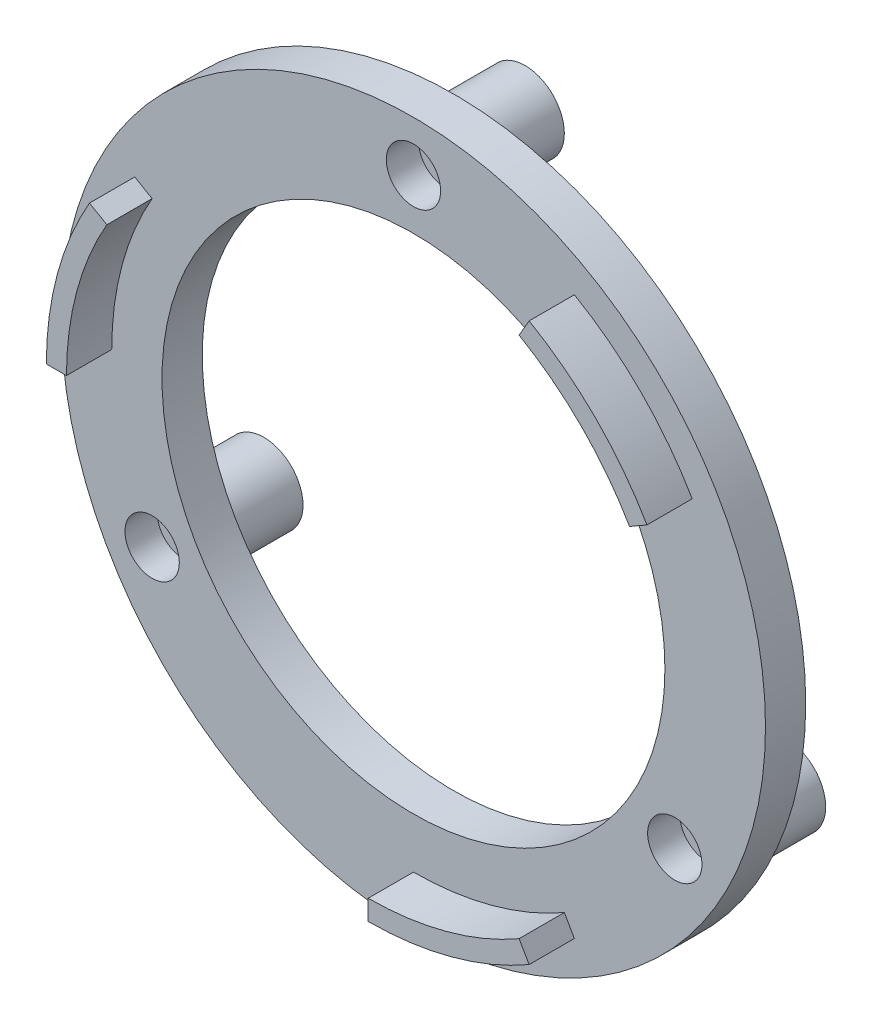
SolidWorks part; units mm, degrees
ref_plane "Front Plane" through (0, 0, 0) normal (0, 0, 1) x (1, 0, 0)
ref_plane "Top Plane" through (0, 0, 0) normal (0, 1, 0) x (1, 0, 0)
ref_plane "Right Plane" through (0, 0, 0) normal (1, 0, 0) x (0, 0, -1)
sketch "Sketch1" plane through (0, 0, 0) normal (0, 0, 1) x (1, 0, 0)
  circle A0 centre (0, 0) radius 30
  circle A1 centre (0, 0) radius 35
  circle A2 centre (0, 0) radius 25
  dimension "D1" = 5
  dimension "D2" = 5
extrude "Boss-Extrude1" add sketch "Sketch1" along normal blind 4 contours A1 A0 | A0 A2
sketch "Sketch2" plane through (0, 0, 0) normal (0, 0, -1) x (-1, 0, 0)
  circle A0 centre (0, 0) radius 30
  circle A1 centre (0, 30) radius 3.9
  circle A5 centre (25.9808, -15) radius 3.9
  circle A6 centre (-25.9808, -15) radius 3.9
  point P12 (0, 0)
  point P14 (0, 0)
  dimension "D1" = 3
extrude "Boss-Extrude2" add sketch "Sketch2" along normal blind 7.1 contours A1 | A6 | A5
sketch "Sketch3" plane through (0, 0, -7.1) normal (0, 0, -1) x (-1, 0, 0)
  circle A0 centre (0, 30) radius 1.6
  circle A4 centre (25.9808, -15) radius 1.6
  circle A5 centre (-25.9808, -15) radius 1.6
  point P10 (0, 0)
  point P12 (0, 0)
  dimension "D1" = 3
extrude "Cut-Extrude1" cut sketch "Sketch3" against normal blind 15
sketch "Sketch4" plane through (0, 0, 4) normal (0, 0, 1) x (1, 0, 0)
  circle A0 centre (0, 30) radius 2.7
  circle A4 centre (25.9808, -15) radius 2.7
  circle A5 centre (-25.9808, -15) radius 2.7
  point P10 (0, 0)
  point P11 (0, 0)
  dimension "D1" = 3
extrude "Cut-Extrude2" cut sketch "Sketch4" against normal blind 3.2
sketch "Sketch6" plane through (0, 0, 4) normal (0, 0, 1) x (1, 0, 0)
  line L0 (32, 0) -> (-32, 0)
  line L1 (0, 0) -> (16, 27.7128)
  line L2 (0, 0) -> (27.7128, 16)
  circle A0 centre (0, 0) radius 32
  circle A1 centre (0, 0) radius 30
  point P7 (0, 0)
extrude "Boss-Extrude3" add sketch "Sketch6" along normal blind 4.5 contours A1 L2 A0 L1
sketch "Sketch7" plane through (0, 0, 4) normal (0, 0, 1) x (1, 0, 0)
  line L0 (16, -27.7128) -> (15, -25.9808)
  line L1 (0, -30) -> (0, -32)
  line L2 (25.9808, 15) -> (27.7128, 16)
  line L3 (16, 27.7128) -> (15, 25.9808)
  line L4 (25.9808, 15) -> (27.7128, 16)
  line L5 (16, 27.7128) -> (15, 25.9808)
  line L6 (-32, 0) -> (-30, 0)
  line L7 (-25.9808, 15) -> (-27.7128, 16)
  arc A0 (0, -30) -> (15, -25.9808) centre (0, 0) ccw
  arc A1 (0, -32) -> (16, -27.7128) centre (0, 0) ccw
  arc A2 (25.9808, 15) -> (15, 25.9808) centre (0, 0) ccw
  arc A3 (27.7128, 16) -> (16, 27.7128) centre (0, 0) ccw
  arc A4 (25.9808, 15) -> (15, 25.9808) centre (0, 0) ccw
  arc A5 (27.7128, 16) -> (16, 27.7128) centre (0, 0) ccw
  arc A6 (-25.9808, 15) -> (-30, 0) centre (0, 0) ccw
  arc A7 (-27.7128, 16) -> (-32, 0) centre (0, 0) ccw
  point P17 (0, 0)
  dimension "D1" = 0
  dimension "D2" = 3
extrude "Boss-Extrude4" add sketch "Sketch7" along normal blind 4.5 contours A4 L5 A5 L4 | L6 A6 L7 A7 | L0 A0 L1 A1
